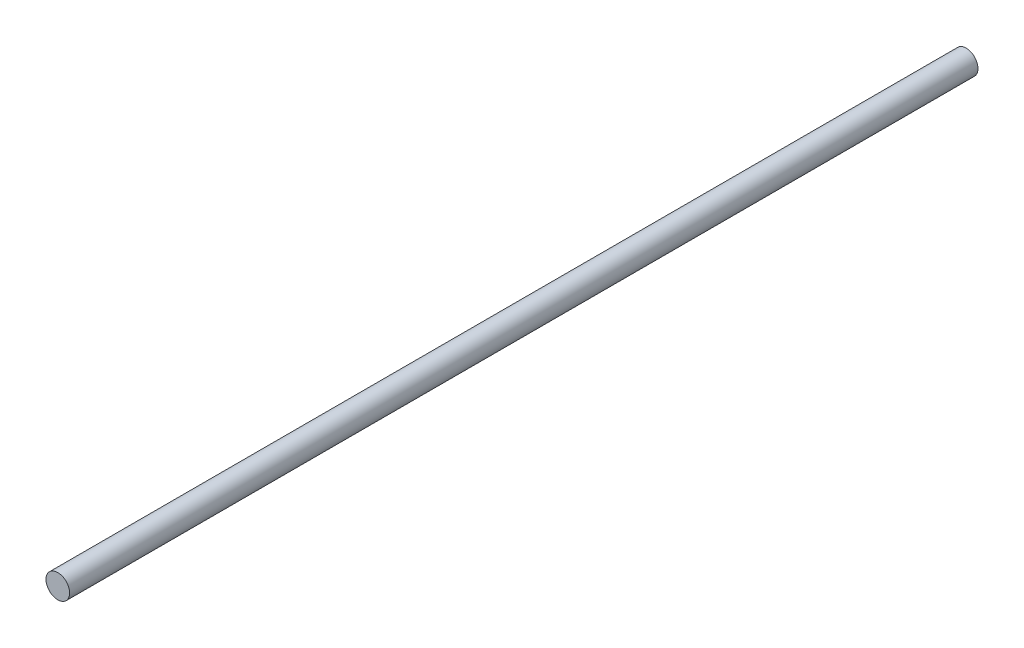
SolidWorks part; units mm, degrees
ref_plane "Front Plane" through (0, 0, 0) normal (0, 0, 1) x (1, 0, 0)
ref_plane "Top Plane" through (0, 0, 0) normal (0, 1, 0) x (1, 0, 0)
ref_plane "Right Plane" through (0, 0, 0) normal (1, 0, 0) x (0, 0, -1)
sketch "Sketch1" plane through (0, 0, 0) normal (0, 0, 1) x (1, 0, 0)
  circle A0 centre (0, 0) radius 3.9688
  dimension "D1" = 7.9375
extrude "Boss-Extrude1" add sketch "Sketch1" along normal blind 304.8
